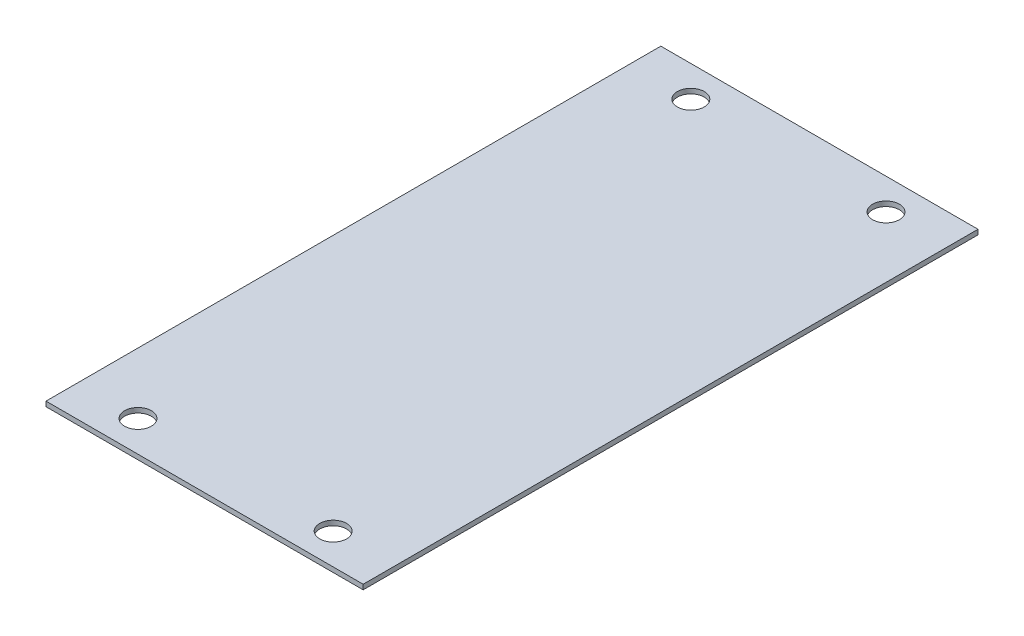
SolidWorks part; units mm, degrees
ref_plane "Front Plane" through (0, 0, 0) normal (0, 0, 1) x (1, 0, 0)
ref_plane "Top Plane" through (0, 0, 0) normal (0, 1, 0) x (1, 0, 0)
ref_plane "Right Plane" through (0, 0, 0) normal (1, 0, 0) x (0, 0, -1)
sketch "Sketch1" plane through (0, 0, 0) normal (0, 1, 0) x (1, 0, 0)
  line L0 (0, -126) -> (0, 126) construction
  line L1 (-65, 126) -> (65, 126)
  line L2 (-65, 126) -> (-65, -126)
  line L3 (-65, -126) -> (65, -126)
  line L4 (65, 126) -> (65, -126)
  line L5 (-65, 126) -> (65, -126) construction
  line L6 (-65, -126) -> (65, 126) construction
  line L8 (-40, -113.3) -> (40, -113.3) construction
  line L9 (-40, -113.3) -> (-40, 113.3) construction
  line L10 (-40, 113.3) -> (40, 113.3) construction
  line L11 (40, -113.3) -> (40, 113.3) construction
  line L12 (-40, -113.3) -> (40, 113.3) construction
  line L13 (-40, 113.3) -> (40, -113.3) construction
  circle A1 centre (-40, 113.3) radius 5.5
  circle A2 centre (40, 113.3) radius 5.5
  circle A3 centre (40, -113.3) radius 5.5
  circle A4 centre (-40, -113.3) radius 5.5
  point P0 (0, 0)
  point P6 (0, 0)
  point P9 (0, 0)
  dimension "D5" = 11
  dimension "D1" = 130
  dimension "D2" = 252
  dimension "D3" = 25
  dimension "D4" = 12.7
extrude "Boss-Extrude1" add sketch "Sketch1" along normal blind 2
